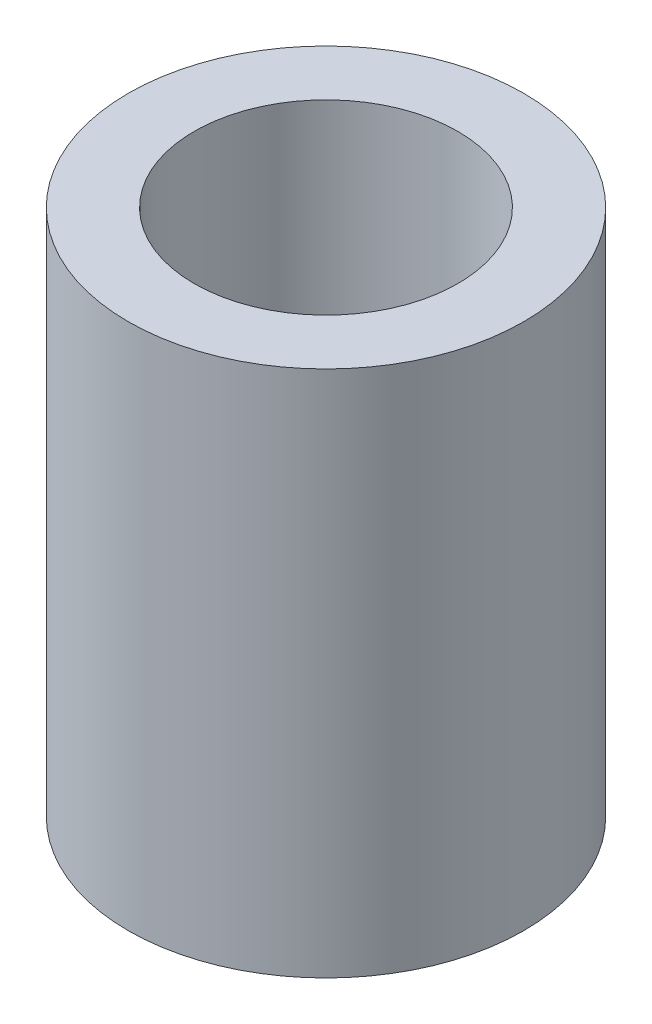
SolidWorks part; units mm, degrees
material "Rubber"
ref_plane "Front Plane" through (0, 0, 0) normal (0, 0, 1) x (1, 0, 0)
ref_plane "Top Plane" through (0, 0, 0) normal (0, 1, 0) x (1, 0, 0)
ref_plane "Right Plane" through (0, 0, 0) normal (1, 0, 0) x (0, 0, -1)
sketch "Sketch1" plane through (0, 0, 0) normal (0, 1, 0) x (1, 0, 0)
  circle A0 centre (0, 0) radius 4.7625
  circle A1 centre (0, 0) radius 3.175
  dimension "D1" = 6.35
  dimension "D2" = 9.525
extrude "Boss-Extrude1" add sketch "Sketch1" along normal blind 12.7
